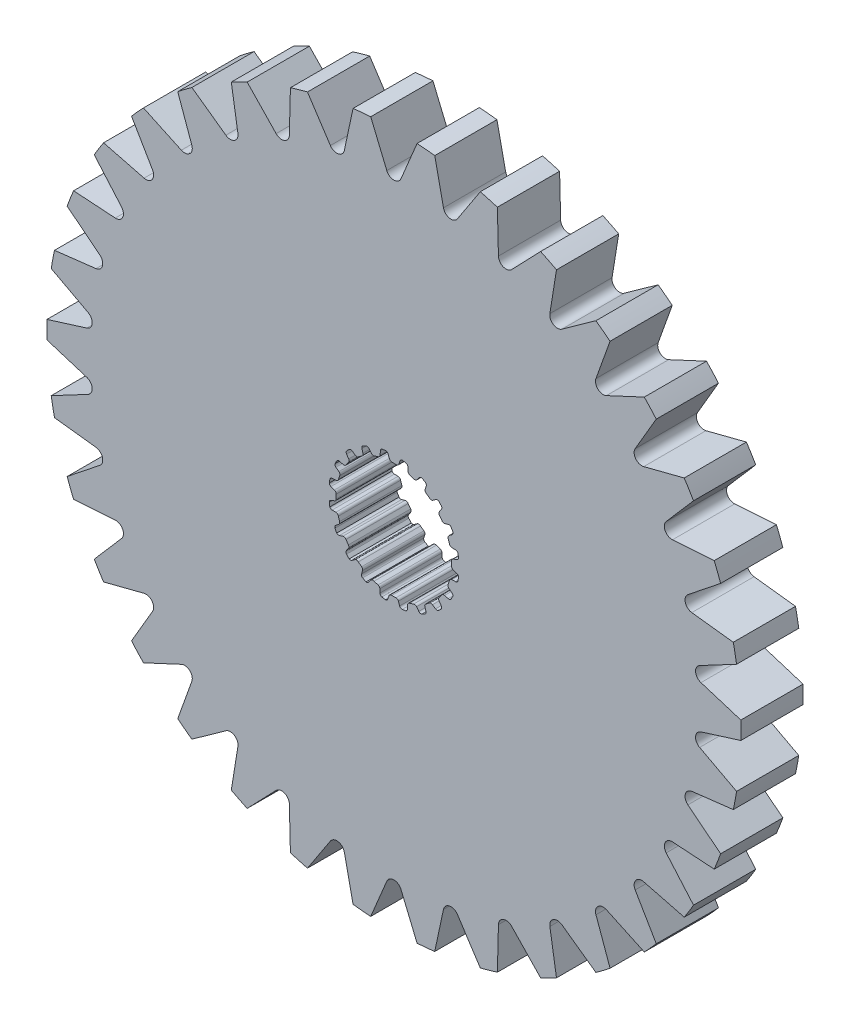
SolidWorks part; units mm, degrees
ref_plane "Front Plane" through (0, 0, 0) normal (0, 0, 1) x (1, 0, 0)
ref_plane "Top Plane" through (0, 0, 0) normal (0, 1, 0) x (1, 0, 0)
ref_plane "Right Plane" through (0, 0, 0) normal (1, 0, 0) x (0, 0, -1)
sketch "Sketch1" plane through (0, 0, 0) normal (0, 0, 1) x (1, 0, 0)
  line L0 (-0.1069, 2.9699) -> (0.1069, 2.9699)
  line L1 (0.3159, 3.2375) -> (0.2537, 3.0575)
  line L2 (-0.2964, 3.2367) -> (-0.2318, 3.0575)
  line L3 (-0.2964, 3.2367) -> (0.3159, 3.2375) construction
  line L4 (0, 3.3252) -> (0, 0) construction
  line L5 (-0.2318, 3.0575) -> (0.2537, 3.0575) construction
  line L6 (-0.4281, 3.3241) -> (0.4281, 3.3263) construction
  line L7 (0.7183, 3.1698) -> (0.7244, 2.9795)
  line L8 (0.816, 2.8576) -> (1.0195, 2.7915)
  line L9 (1.3009, 2.9815) -> (1.1862, 2.8295)
  line L10 (1.6627, 2.7927) -> (1.6097, 2.6099)
  line L11 (1.6591, 2.4655) -> (1.8322, 2.3398)
  line L12 (2.1585, 2.4335) -> (2.0025, 2.3245)
  line L13 (2.4443, 2.1423) -> (2.3374, 1.9847)
  line L14 (2.3398, 1.8322) -> (2.4655, 1.6591)
  line L15 (2.8049, 1.6474) -> (2.6228, 1.5919)
  line L16 (2.9866, 1.2821) -> (2.8363, 1.1653)
  line L17 (2.7915, 1.0195) -> (2.8576, 0.816)
  line L18 (3.1767, 0.7) -> (2.9863, 0.7035)
  line L19 (3.2367, 0.2964) -> (3.0575, 0.2318)
  line L20 (2.9699, 0.1069) -> (2.9699, -0.1069)
  line L21 (3.2375, -0.3159) -> (3.0575, -0.2537)
  line L22 (3.1698, -0.7183) -> (2.9795, -0.7244)
  line L23 (2.8576, -0.816) -> (2.7915, -1.0195)
  line L24 (2.9815, -1.3009) -> (2.8295, -1.1862)
  line L25 (2.7927, -1.6627) -> (2.6099, -1.6097)
  line L26 (2.4655, -1.6591) -> (2.3398, -1.8322)
  line L27 (2.4335, -2.1585) -> (2.3245, -2.0025)
  line L28 (2.1423, -2.4443) -> (1.9847, -2.3374)
  line L29 (1.8322, -2.3398) -> (1.6591, -2.4655)
  line L30 (1.6474, -2.8049) -> (1.5919, -2.6228)
  line L31 (1.2821, -2.9866) -> (1.1653, -2.8363)
  line L32 (1.0195, -2.7915) -> (0.816, -2.8576)
  line L33 (0.7, -3.1767) -> (0.7035, -2.9863)
  line L34 (0.2964, -3.2367) -> (0.2318, -3.0575)
  line L35 (0.1069, -2.9699) -> (-0.1069, -2.9699)
  line L36 (-0.3159, -3.2375) -> (-0.2537, -3.0575)
  line L37 (-0.7183, -3.1698) -> (-0.7244, -2.9795)
  line L38 (-0.816, -2.8576) -> (-1.0195, -2.7915)
  line L39 (-1.3009, -2.9815) -> (-1.1862, -2.8295)
  line L40 (-1.6627, -2.7927) -> (-1.6097, -2.6099)
  line L41 (-1.6591, -2.4655) -> (-1.8322, -2.3398)
  line L42 (-2.1585, -2.4335) -> (-2.0025, -2.3245)
  line L43 (-2.4443, -2.1423) -> (-2.3374, -1.9847)
  line L44 (-2.3398, -1.8322) -> (-2.4655, -1.6591)
  line L45 (-2.8049, -1.6474) -> (-2.6228, -1.5919)
  line L46 (-2.9866, -1.2821) -> (-2.8363, -1.1653)
  line L47 (-2.7915, -1.0195) -> (-2.8576, -0.816)
  line L48 (-3.1767, -0.7) -> (-2.9863, -0.7035)
  line L49 (-3.2367, -0.2964) -> (-3.0575, -0.2318)
  line L50 (-2.9699, -0.1069) -> (-2.9699, 0.1069)
  line L51 (-3.2375, 0.3159) -> (-3.0575, 0.2537)
  line L52 (-3.1698, 0.7183) -> (-2.9795, 0.7244)
  line L53 (-2.8576, 0.816) -> (-2.7915, 1.0195)
  line L54 (-2.9815, 1.3009) -> (-2.8295, 1.1862)
  line L55 (-2.7927, 1.6627) -> (-2.6099, 1.6097)
  line L56 (-2.4655, 1.6591) -> (-2.3398, 1.8322)
  line L57 (-2.4335, 2.1585) -> (-2.3245, 2.0025)
  line L58 (-2.1423, 2.4443) -> (-1.9847, 2.3374)
  line L59 (-1.8322, 2.3398) -> (-1.6591, 2.4655)
  line L60 (-1.6474, 2.8049) -> (-1.5919, 2.6228)
  line L61 (-1.2821, 2.9866) -> (-1.1653, 2.8363)
  line L62 (-1.0195, 2.7915) -> (-0.816, 2.8576)
  line L63 (-0.7, 3.1767) -> (-0.7035, 2.9863)
  line L64 (0.4281, 3.3263) -> (0.62, 3.2938)
  line L65 (1.4351, 3.0312) -> (1.6075, 2.9409)
  line L66 (2.3015, 2.4394) -> (2.4376, 2.3003)
  line L67 (2.9427, 1.6088) -> (3.0291, 1.4344)
  line L68 (3.2958, 0.6207) -> (3.3241, 0.4281)
  line L69 (3.3263, -0.4281) -> (3.2938, -0.62)
  line L70 (3.0312, -1.4351) -> (2.9409, -1.6075)
  line L71 (2.4394, -2.3015) -> (2.3003, -2.4376)
  line L72 (1.6088, -2.9427) -> (1.4344, -3.0291)
  line L73 (0.6207, -3.2958) -> (0.4281, -3.3241)
  line L74 (-0.4281, -3.3263) -> (-0.62, -3.2938)
  line L75 (-1.4351, -3.0312) -> (-1.6075, -2.9409)
  line L76 (-2.3015, -2.4394) -> (-2.4376, -2.3003)
  line L77 (-2.9427, -1.6088) -> (-3.0291, -1.4344)
  line L78 (-3.2958, -0.6207) -> (-3.3241, -0.4281)
  line L79 (-3.3263, 0.4281) -> (-3.2938, 0.62)
  line L80 (-3.0312, 1.4351) -> (-2.9409, 1.6075)
  line L81 (-2.4394, 2.3015) -> (-2.3003, 2.4376)
  line L82 (-1.6088, 2.9427) -> (-1.4344, 3.0291)
  line L83 (-0.6207, 3.2958) -> (-0.4281, 3.3241)
  arc A0 (0.2537, 3.0575) -> (0.1069, 2.9699) centre (0.1283, 3.1009) cw
  arc A1 (-0.2318, 3.0575) -> (-0.1069, 2.9699) centre (-0.1069, 3.1026) ccw
  arc A2 (0.62, 3.2938) -> (0.7183, 3.1698) centre (0.5856, 3.1656) cw
  arc A3 (0.7244, 2.9795) -> (0.816, 2.8576) centre (0.857, 2.9838) ccw
  arc A4 (-0.4281, 3.3241) -> (-0.2964, 3.2367) centre (-0.4213, 3.1916) cw
  arc A5 (0.4281, 3.3263) -> (0.3159, 3.2375) centre (0.4413, 3.1942) ccw
  arc A6 (1.1862, 2.8295) -> (1.0195, 2.7915) centre (1.0802, 2.9095) cw
  arc A7 (1.4351, 3.0312) -> (1.3009, 2.9815) centre (1.4068, 2.9015) ccw
  arc A8 (1.6075, 2.9409) -> (1.6627, 2.7927) centre (1.5352, 2.8297) cw
  arc A9 (1.6097, 2.6099) -> (1.6591, 2.4655) centre (1.7371, 2.5729) ccw
  arc A10 (2.0025, 2.3245) -> (1.8322, 2.3398) centre (1.9264, 2.4332) cw
  arc A11 (2.3015, 2.4394) -> (2.1585, 2.4335) centre (2.2346, 2.3248) ccw
  arc A12 (2.4376, 2.3003) -> (2.4443, 2.1423) centre (2.3345, 2.2168) cw
  arc A13 (2.3374, 1.9847) -> (2.3398, 1.8322) centre (2.4472, 1.9102) ccw
  arc A14 (2.6228, 1.5919) -> (2.4655, 1.6591) centre (2.5841, 1.7189) cw
  arc A15 (2.9427, 1.6088) -> (2.8049, 1.6474) centre (2.8436, 1.5205) ccw
  arc A16 (3.0291, 1.4344) -> (2.9866, 1.2821) centre (2.9052, 1.3869) cw
  arc A17 (2.8363, 1.1653) -> (2.7915, 1.0195) centre (2.9177, 1.0605) ccw
  arc A18 (2.9863, 0.7035) -> (2.8576, 0.816) centre (2.9887, 0.8362) cw
  arc A19 (3.2958, 0.6207) -> (3.1767, 0.7) centre (3.1743, 0.5673) ccw
  arc A20 (3.3241, 0.4281) -> (3.2367, 0.2964) centre (3.1916, 0.4213) cw
  arc A21 (3.0575, 0.2318) -> (2.9699, 0.1069) centre (3.1026, 0.1069) ccw
  arc A22 (3.0575, -0.2537) -> (2.9699, -0.1069) centre (3.1009, -0.1283) cw
  arc A23 (3.3263, -0.4281) -> (3.2375, -0.3159) centre (3.1942, -0.4413) ccw
  arc A24 (3.2938, -0.62) -> (3.1698, -0.7183) centre (3.1656, -0.5856) cw
  arc A25 (2.9795, -0.7244) -> (2.8576, -0.816) centre (2.9838, -0.857) ccw
  arc A26 (2.8295, -1.1862) -> (2.7915, -1.0195) centre (2.9095, -1.0802) cw
  arc A27 (3.0312, -1.4351) -> (2.9815, -1.3009) centre (2.9015, -1.4068) ccw
  arc A28 (2.9409, -1.6075) -> (2.7927, -1.6627) centre (2.8297, -1.5352) cw
  arc A29 (2.6099, -1.6097) -> (2.4655, -1.6591) centre (2.5729, -1.7371) ccw
  arc A30 (2.3245, -2.0025) -> (2.3398, -1.8322) centre (2.4332, -1.9264) cw
  arc A31 (2.4394, -2.3015) -> (2.4335, -2.1585) centre (2.3248, -2.2346) ccw
  arc A32 (2.3003, -2.4376) -> (2.1423, -2.4443) centre (2.2168, -2.3345) cw
  arc A33 (1.9847, -2.3374) -> (1.8322, -2.3398) centre (1.9102, -2.4472) ccw
  arc A34 (1.5919, -2.6228) -> (1.6591, -2.4655) centre (1.7189, -2.5841) cw
  arc A35 (1.6088, -2.9427) -> (1.6474, -2.8049) centre (1.5205, -2.8436) ccw
  arc A36 (1.4344, -3.0291) -> (1.2821, -2.9866) centre (1.3869, -2.9052) cw
  arc A37 (1.1653, -2.8363) -> (1.0195, -2.7915) centre (1.0605, -2.9177) ccw
  arc A38 (0.7035, -2.9863) -> (0.816, -2.8576) centre (0.8362, -2.9887) cw
  arc A39 (0.6207, -3.2958) -> (0.7, -3.1767) centre (0.5673, -3.1743) ccw
  arc A40 (0.4281, -3.3241) -> (0.2964, -3.2367) centre (0.4213, -3.1916) cw
  arc A41 (0.2318, -3.0575) -> (0.1069, -2.9699) centre (0.1069, -3.1026) ccw
  arc A42 (-0.2537, -3.0575) -> (-0.1069, -2.9699) centre (-0.1283, -3.1009) cw
  arc A43 (-0.4281, -3.3263) -> (-0.3159, -3.2375) centre (-0.4413, -3.1942) ccw
  arc A44 (-0.62, -3.2938) -> (-0.7183, -3.1698) centre (-0.5856, -3.1656) cw
  arc A45 (-0.7244, -2.9795) -> (-0.816, -2.8576) centre (-0.857, -2.9838) ccw
  arc A46 (-1.1862, -2.8295) -> (-1.0195, -2.7915) centre (-1.0802, -2.9095) cw
  arc A47 (-1.4351, -3.0312) -> (-1.3009, -2.9815) centre (-1.4068, -2.9015) ccw
  arc A48 (-1.6075, -2.9409) -> (-1.6627, -2.7927) centre (-1.5352, -2.8297) cw
  arc A49 (-1.6097, -2.6099) -> (-1.6591, -2.4655) centre (-1.7371, -2.5729) ccw
  arc A50 (-2.0025, -2.3245) -> (-1.8322, -2.3398) centre (-1.9264, -2.4332) cw
  arc A51 (-2.3015, -2.4394) -> (-2.1585, -2.4335) centre (-2.2346, -2.3248) ccw
  arc A52 (-2.4376, -2.3003) -> (-2.4443, -2.1423) centre (-2.3345, -2.2168) cw
  arc A53 (-2.3374, -1.9847) -> (-2.3398, -1.8322) centre (-2.4472, -1.9102) ccw
  arc A54 (-2.6228, -1.5919) -> (-2.4655, -1.6591) centre (-2.5841, -1.7189) cw
  arc A55 (-2.9427, -1.6088) -> (-2.8049, -1.6474) centre (-2.8436, -1.5205) ccw
  arc A56 (-3.0291, -1.4344) -> (-2.9866, -1.2821) centre (-2.9052, -1.3869) cw
  arc A57 (-2.8363, -1.1653) -> (-2.7915, -1.0195) centre (-2.9177, -1.0605) ccw
  arc A58 (-2.9863, -0.7035) -> (-2.8576, -0.816) centre (-2.9887, -0.8362) cw
  arc A59 (-3.2958, -0.6207) -> (-3.1767, -0.7) centre (-3.1743, -0.5673) ccw
  arc A60 (-3.3241, -0.4281) -> (-3.2367, -0.2964) centre (-3.1916, -0.4213) cw
  arc A61 (-3.0575, -0.2318) -> (-2.9699, -0.1069) centre (-3.1026, -0.1069) ccw
  arc A62 (-3.0575, 0.2537) -> (-2.9699, 0.1069) centre (-3.1009, 0.1283) cw
  arc A63 (-3.3263, 0.4281) -> (-3.2375, 0.3159) centre (-3.1942, 0.4413) ccw
  arc A64 (-3.2938, 0.62) -> (-3.1698, 0.7183) centre (-3.1656, 0.5856) cw
  arc A65 (-2.9795, 0.7244) -> (-2.8576, 0.816) centre (-2.9838, 0.857) ccw
  arc A66 (-2.8295, 1.1862) -> (-2.7915, 1.0195) centre (-2.9095, 1.0802) cw
  arc A67 (-3.0312, 1.4351) -> (-2.9815, 1.3009) centre (-2.9015, 1.4068) ccw
  arc A68 (-2.9409, 1.6075) -> (-2.7927, 1.6627) centre (-2.8297, 1.5352) cw
  arc A69 (-2.6099, 1.6097) -> (-2.4655, 1.6591) centre (-2.5729, 1.7371) ccw
  arc A70 (-2.3245, 2.0025) -> (-2.3398, 1.8322) centre (-2.4332, 1.9264) cw
  arc A71 (-2.4394, 2.3015) -> (-2.4335, 2.1585) centre (-2.3248, 2.2346) ccw
  arc A72 (-2.3003, 2.4376) -> (-2.1423, 2.4443) centre (-2.2168, 2.3345) cw
  arc A73 (-1.9847, 2.3374) -> (-1.8322, 2.3398) centre (-1.9102, 2.4472) ccw
  arc A74 (-1.5919, 2.6228) -> (-1.6591, 2.4655) centre (-1.7189, 2.5841) cw
  arc A75 (-1.6088, 2.9427) -> (-1.6474, 2.8049) centre (-1.5205, 2.8436) ccw
  arc A76 (-1.4344, 3.0291) -> (-1.2821, 2.9866) centre (-1.3869, 2.9052) cw
  arc A77 (-1.1653, 2.8363) -> (-1.0195, 2.7915) centre (-1.0605, 2.9177) ccw
  arc A78 (-0.7035, 2.9863) -> (-0.816, 2.8576) centre (-0.8362, 2.9887) cw
  arc A79 (-0.6207, 3.2958) -> (-0.7, 3.1767) centre (-0.5673, 3.1743) ccw
  circle A80 centre (0, 0) radius 17.8524
  point P14 (0, 2.9699)
  point P247 (0, 0)
  dimension "D4" = 0.1327
  dimension "D8" = 20
  dimension "D9" = 35.7048
  dimension "D1" = 2.9699
  dimension "D2" = 0.2139
  dimension "D3" = 0.1904
  dimension "D5" = 0.0877
  dimension "D6" = 0.4855
  dimension "D7" = 0.8563
extrude "Boss-Extrude1" add sketch "Sketch1" along normal mid plane 3.2004
sketch "Sketch2" plane through (0, 0, 1.6002) normal (0, 0, 1) x (1, 0, 0)
  line L0 (0, 17.8125) -> (0, 0) construction
  line L1 (1.557, 33.6415) -> (0, 0) construction
  line L2 (-1.1924, 17.8125) -> (1.1924, 17.8125) construction
  line L3 (-0.7785, 16.8207) -> (0.7785, 16.8207) construction
  line L4 (-1.1924, 17.8125) -> (-0.3646, 15.8289)
  line L5 (1.1924, 17.8125) -> (0.3646, 15.8289)
  line L6 (4.4451, 17.2901) -> (3.267, 15.4924)
  line L7 (2.101, 17.7283) -> (2.5501, 15.6264)
  line L8 (7.5465, 16.179) -> (6.0581, 14.6283)
  line L9 (5.3228, 17.0404) -> (5.378, 14.8918)
  line L10 (10.3909, 14.5168) -> (8.6429, 13.2661)
  line L11 (8.3633, 15.7722) -> (8.0228, 13.65)
  line L12 (12.8814, 12.3603) -> (10.9334, 11.4521)
  line L13 (11.1191, 13.9669) -> (10.3944, 11.9434)
  line L14 (14.9333, 9.7829) -> (12.8515, 9.2481)
  line L15 (13.4961, 11.686) -> (12.412, 9.8301)
  line L16 (16.4766, 6.8724) -> (14.332, 6.7291)
  line L17 (15.4136, 9.0071) -> (14.0069, 7.382)
  line L18 (17.4589, 3.7278) -> (15.3245, 3.9811)
  line L19 (16.8062, 6.0215) -> (15.1249, 4.6825)
  line L20 (17.8466, 0.4562) -> (15.7951, 1.0974)
  line L21 (17.6265, 2.8308) -> (15.7278, 1.8236)
  line L22 (17.6265, -2.8308) -> (15.7278, -1.8236)
  line L23 (17.8466, -0.4562) -> (15.7951, -1.0974)
  line L24 (16.8062, -6.0215) -> (15.1249, -4.6825)
  line L25 (17.4589, -3.7278) -> (15.3245, -3.9811)
  line L26 (15.4136, -9.0071) -> (14.0069, -7.382)
  line L27 (16.4766, -6.8724) -> (14.332, -6.7291)
  line L28 (13.4961, -11.686) -> (12.412, -9.8301)
  line L29 (14.9333, -9.7829) -> (12.8515, -9.2481)
  line L30 (11.1191, -13.9669) -> (10.3944, -11.9434)
  line L31 (12.8814, -12.3603) -> (10.9334, -11.4521)
  line L32 (8.3633, -15.7722) -> (8.0228, -13.65)
  line L33 (10.3909, -14.5168) -> (8.6429, -13.2661)
  line L34 (5.3228, -17.0404) -> (5.378, -14.8918)
  line L35 (7.5465, -16.179) -> (6.0581, -14.6283)
  line L36 (2.101, -17.7283) -> (2.5501, -15.6264)
  line L37 (4.4451, -17.2901) -> (3.267, -15.4924)
  line L38 (-1.1924, -17.8125) -> (-0.3646, -15.8289)
  line L39 (1.1924, -17.8125) -> (0.3646, -15.8289)
  line L40 (-4.4451, -17.2901) -> (-3.267, -15.4924)
  line L41 (-2.101, -17.7283) -> (-2.5501, -15.6264)
  line L42 (-7.5465, -16.179) -> (-6.0581, -14.6283)
  line L43 (-5.3228, -17.0404) -> (-5.378, -14.8918)
  line L44 (-10.3909, -14.5168) -> (-8.6429, -13.2661)
  line L45 (-8.3633, -15.7722) -> (-8.0228, -13.65)
  line L46 (-12.8814, -12.3603) -> (-10.9334, -11.4521)
  line L47 (-11.1191, -13.9669) -> (-10.3944, -11.9434)
  line L48 (-14.9333, -9.7829) -> (-12.8515, -9.2481)
  line L49 (-13.4961, -11.686) -> (-12.412, -9.8301)
  line L50 (-16.4766, -6.8724) -> (-14.332, -6.7291)
  line L51 (-15.4136, -9.0071) -> (-14.0069, -7.382)
  line L52 (-17.4589, -3.7278) -> (-15.3245, -3.9811)
  line L53 (-16.8062, -6.0215) -> (-15.1249, -4.6825)
  line L54 (-17.8466, -0.4562) -> (-15.7951, -1.0974)
  line L55 (-17.6265, -2.8308) -> (-15.7278, -1.8236)
  line L56 (-17.6265, 2.8308) -> (-15.7278, 1.8236)
  line L57 (-17.8466, 0.4562) -> (-15.7951, 1.0974)
  line L58 (-16.8062, 6.0215) -> (-15.1249, 4.6825)
  line L59 (-17.4589, 3.7278) -> (-15.3245, 3.9811)
  line L60 (-15.4136, 9.0071) -> (-14.0069, 7.382)
  line L61 (-16.4766, 6.8724) -> (-14.332, 6.7291)
  line L62 (-13.4961, 11.686) -> (-12.412, 9.8301)
  line L63 (-14.9333, 9.7829) -> (-12.8515, 9.2481)
  line L64 (-11.1191, 13.9669) -> (-10.3944, 11.9434)
  line L65 (-12.8814, 12.3603) -> (-10.9334, 11.4521)
  line L66 (-8.3633, 15.7722) -> (-8.0228, 13.65)
  line L67 (-10.3909, 14.5168) -> (-8.6429, 13.2661)
  line L68 (-5.3228, 17.0404) -> (-5.378, 14.8918)
  line L69 (-7.5465, 16.179) -> (-6.0581, 14.6283)
  line L70 (-2.101, 17.7283) -> (-2.5501, 15.6264)
  line L71 (-4.4451, 17.2901) -> (-3.267, 15.4924)
  circle A0 centre (0, 0) radius 17.8524 construction
  arc A1 (-0.3646, 15.8289) -> (0.3646, 15.8289) centre (0, 15.9811) ccw
  arc A2 (-1.1924, 17.8125) -> (1.1924, 17.8125) centre (0, 0) cw
  arc A3 (2.101, 17.7283) -> (4.4451, 17.2901) centre (0, 0) cw
  arc A4 (2.5501, 15.6264) -> (3.267, 15.4924) centre (2.9365, 15.709) ccw
  arc A5 (5.3228, 17.0404) -> (7.5465, 16.179) centre (0, 0) cw
  arc A6 (5.378, 14.8918) -> (6.0581, 14.6283) centre (5.773, 14.9019) ccw
  arc A7 (8.3633, 15.7722) -> (10.3909, 14.5168) centre (0, 0) cw
  arc A8 (8.0228, 13.65) -> (8.6429, 13.2661) centre (8.413, 13.5874) ccw
  arc A9 (11.1191, 13.9669) -> (12.8814, 12.3603) centre (0, 0) cw
  arc A10 (10.3944, 11.9434) -> (10.9334, 11.4521) centre (10.7664, 11.8102) ccw
  arc A11 (13.4961, 11.686) -> (14.9333, 9.7829) centre (0, 0) cw
  arc A12 (12.412, 9.8301) -> (12.8515, 9.2481) centre (12.7532, 9.6308) ccw
  arc A13 (15.4136, 9.0071) -> (16.4766, 6.8724) centre (0, 0) cw
  arc A14 (14.0069, 7.382) -> (14.332, 6.7291) centre (14.3057, 7.1234) ccw
  arc A15 (16.8062, 6.0215) -> (17.4589, 3.7278) centre (0, 0) cw
  arc A16 (15.1249, 4.6825) -> (15.3245, 3.9811) centre (15.371, 4.3734) ccw
  arc A17 (17.6265, 2.8308) -> (17.8466, 0.4562) centre (0, 0) cw
  arc A18 (15.7278, 1.8236) -> (15.7951, 1.0974) centre (15.9129, 1.4745) ccw
  arc A19 (17.8466, -0.4562) -> (17.6265, -2.8308) centre (0, 0) cw
  arc A20 (15.7951, -1.0974) -> (15.7278, -1.8236) centre (15.9129, -1.4745) ccw
  arc A21 (17.4589, -3.7278) -> (16.8062, -6.0215) centre (0, 0) cw
  arc A22 (15.3245, -3.9811) -> (15.1249, -4.6825) centre (15.371, -4.3734) ccw
  arc A23 (16.4766, -6.8724) -> (15.4136, -9.0071) centre (0, 0) cw
  arc A24 (14.332, -6.7291) -> (14.0069, -7.382) centre (14.3057, -7.1234) ccw
  arc A25 (14.9333, -9.7829) -> (13.4961, -11.686) centre (0, 0) cw
  arc A26 (12.8515, -9.2481) -> (12.412, -9.8301) centre (12.7532, -9.6308) ccw
  arc A27 (12.8814, -12.3603) -> (11.1191, -13.9669) centre (0, 0) cw
  arc A28 (10.9334, -11.4521) -> (10.3944, -11.9434) centre (10.7664, -11.8102) ccw
  arc A29 (10.3909, -14.5168) -> (8.3633, -15.7722) centre (0, 0) cw
  arc A30 (8.6429, -13.2661) -> (8.0228, -13.65) centre (8.413, -13.5874) ccw
  arc A31 (7.5465, -16.179) -> (5.3228, -17.0404) centre (0, 0) cw
  arc A32 (6.0581, -14.6283) -> (5.378, -14.8918) centre (5.773, -14.9019) ccw
  arc A33 (4.4451, -17.2901) -> (2.101, -17.7283) centre (0, 0) cw
  arc A34 (3.267, -15.4924) -> (2.5501, -15.6264) centre (2.9365, -15.709) ccw
  arc A35 (1.1924, -17.8125) -> (-1.1924, -17.8125) centre (0, 0) cw
  arc A36 (0.3646, -15.8289) -> (-0.3646, -15.8289) centre (0, -15.9811) ccw
  arc A37 (-2.101, -17.7283) -> (-4.4451, -17.2901) centre (0, 0) cw
  arc A38 (-2.5501, -15.6264) -> (-3.267, -15.4924) centre (-2.9365, -15.709) ccw
  arc A39 (-5.3228, -17.0404) -> (-7.5465, -16.179) centre (0, 0) cw
  arc A40 (-5.378, -14.8918) -> (-6.0581, -14.6283) centre (-5.773, -14.9019) ccw
  arc A41 (-8.3633, -15.7722) -> (-10.3909, -14.5168) centre (0, 0) cw
  arc A42 (-8.0228, -13.65) -> (-8.6429, -13.2661) centre (-8.413, -13.5874) ccw
  arc A43 (-11.1191, -13.9669) -> (-12.8814, -12.3603) centre (0, 0) cw
  arc A44 (-10.3944, -11.9434) -> (-10.9334, -11.4521) centre (-10.7664, -11.8102) ccw
  arc A45 (-13.4961, -11.686) -> (-14.9333, -9.7829) centre (0, 0) cw
  arc A46 (-12.412, -9.8301) -> (-12.8515, -9.2481) centre (-12.7532, -9.6308) ccw
  arc A47 (-15.4136, -9.0071) -> (-16.4766, -6.8724) centre (0, 0) cw
  arc A48 (-14.0069, -7.382) -> (-14.332, -6.7291) centre (-14.3057, -7.1234) ccw
  arc A49 (-16.8062, -6.0215) -> (-17.4589, -3.7278) centre (0, 0) cw
  arc A50 (-15.1249, -4.6825) -> (-15.3245, -3.9811) centre (-15.371, -4.3734) ccw
  arc A51 (-17.6265, -2.8308) -> (-17.8466, -0.4562) centre (0, 0) cw
  arc A52 (-15.7278, -1.8236) -> (-15.7951, -1.0974) centre (-15.9129, -1.4745) ccw
  arc A53 (-17.8466, 0.4562) -> (-17.6265, 2.8308) centre (0, 0) cw
  arc A54 (-15.7951, 1.0974) -> (-15.7278, 1.8236) centre (-15.9129, 1.4745) ccw
  arc A55 (-17.4589, 3.7278) -> (-16.8062, 6.0215) centre (0, 0) cw
  arc A56 (-15.3245, 3.9811) -> (-15.1249, 4.6825) centre (-15.371, 4.3734) ccw
  arc A57 (-16.4766, 6.8724) -> (-15.4136, 9.0071) centre (0, 0) cw
  arc A58 (-14.332, 6.7291) -> (-14.0069, 7.382) centre (-14.3057, 7.1234) ccw
  arc A59 (-14.9333, 9.7829) -> (-13.4961, 11.686) centre (0, 0) cw
  arc A60 (-12.8515, 9.2481) -> (-12.412, 9.8301) centre (-12.7532, 9.6308) ccw
  arc A61 (-12.8814, 12.3603) -> (-11.1191, 13.9669) centre (0, 0) cw
  arc A62 (-10.9334, 11.4521) -> (-10.3944, 11.9434) centre (-10.7664, 11.8102) ccw
  arc A63 (-10.3909, 14.5168) -> (-8.3633, 15.7722) centre (0, 0) cw
  arc A64 (-8.6429, 13.2661) -> (-8.0228, 13.65) centre (-8.413, 13.5874) ccw
  arc A65 (-7.5465, 16.179) -> (-5.3228, 17.0404) centre (0, 0) cw
  arc A66 (-6.0581, 14.6283) -> (-5.378, 14.8918) centre (-5.773, 14.9019) ccw
  arc A67 (-4.4451, 17.2901) -> (-2.101, 17.7283) centre (0, 0) cw
  arc A68 (-3.267, 15.4924) -> (-2.5501, 15.6264) centre (-2.9365, 15.709) ccw
  point P9 (0, 16.8207)
  point P171 (0, 0)
  dimension "D1" = 0.9918
  dimension "D2" = 1.557
  dimension "D3" = 20
  dimension "D4" = 34
extrude "Cut-Extrude1" cut sketch "Sketch2" against normal up to surface (3.2004 mm away) up to face at (17.8524, 0, -1.6002)
sketch "Sketch3" plane through (0, 0, 1.6002) normal (0, 0, 1) x (1, 0, 0)
  circle A0 centre (0, 0) radius 16.8606 construction
  circle A1 centre (0, 0) radius 17.8524 construction
  dimension "D1" = 33.7212
